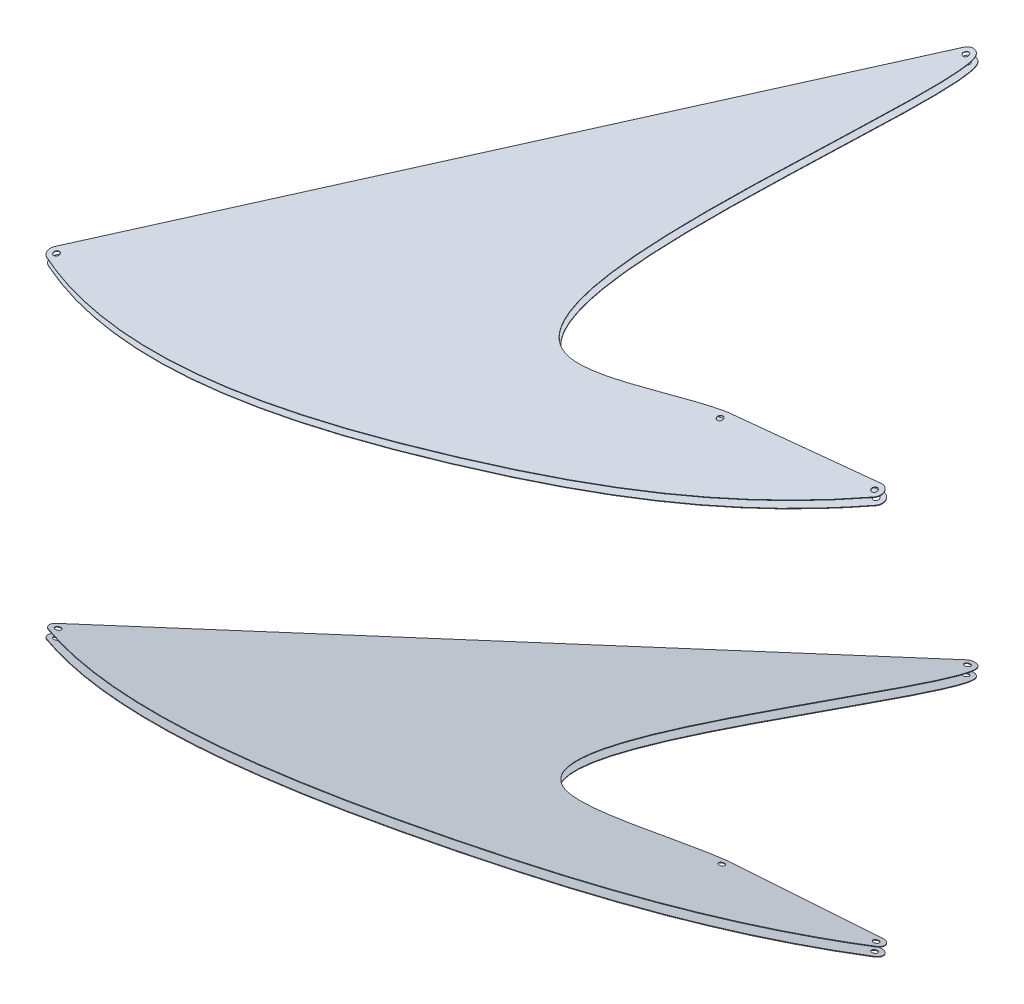
SolidWorks part; units mm, degrees
material "Thornel Mat VMA"
ref_plane "Płaszczyzna XY" through (0, 0, 0) normal (0, 0, 1) x (1, 0, 0)
ref_plane "Płaszczyzna XZ" through (0, 0, 0) normal (0, 1, 0) x (1, 0, 0)
ref_plane "Płaszczyzna YZ" through (0, 0, 0) normal (1, 0, 0) x (0, 0, -1)
sketch "Szkic1" plane through (0, -365.9457, 71.1326) normal (0, -0.9816, 0.1908) x (1, 0, 0)
  line L2 (1483.1737, 808.8534) -> (1634.8716, 794.9597)
  line L3 (939.3713, 984.0725) -> (1348.4905, 414.167)
  line L4 (1483.1737, 808.8534) -> (1634.8716, 794.9597)
  line L5 (939.3713, 984.0725) -> (1348.4905, 414.167)
  circle A0 centre (1354.9893, 418.8323) radius 3 construction
  circle A1 centre (945.8701, 988.7378) radius 3 construction
  circle A2 centre (1634.8716, 802.9597) radius 3 construction
  arc A3 (1634.8716, 794.9597) -> (1640.2813, 808.8534) centre (1634.8716, 802.9597) ccw
  arc A4 (942.8113, 996.1299) -> (939.3713, 984.0725) centre (945.8701, 988.7378) ccw
  arc A5 (1348.4905, 414.167) -> (1362.2836, 415.547) centre (1354.9893, 418.8323) ccw
  arc A6 (1634.8716, 794.9597) -> (1640.2813, 808.8534) centre (1634.8716, 802.9597) ccw
  arc A7 (942.8113, 996.1299) -> (939.3713, 984.0725) centre (945.8701, 988.7378) ccw
  arc A8 (1348.4905, 414.167) -> (1362.2836, 415.547) centre (1354.9893, 418.8323) ccw
  circle A9 centre (1483.9034, 816.82) radius 3 construction
  circle A10 centre (1354.9893, 418.8323) radius 3
  circle A11 centre (945.8701, 988.7378) radius 3
  circle A12 centre (1634.8716, 802.9597) radius 3
  circle A13 centre (1483.9034, 816.82) radius 3
  spline S2 degree 3 poles (1520.5342, -3126.9675) (2189.7267, 400.5932) (1623.1132, 1133.0097) (131.586, 1143.129) (1370.7562, -2890.8231) knots -1.798861 -1.798861 -1.798861 -1.798861 0.451675 2.51583 2.51583 2.51583 2.51583 only from (1640.2813, 808.8534) to (942.8113, 996.1299)
  spline S3 degree 3 poles (-593.8451, 3903.582) (1564.5938, -68.6382) (1362.4748, 333.0797) (1238.3707, 1132.1156) (2251.5927, 131.511) (-793.1853, 4086.8611) knots -1.060105 -1.060105 -1.060105 -1.060105 0.358357 0.741721 1.892324 1.892324 1.892324 1.892324 only from (1362.2836, 415.547) to (1483.1737, 808.8534)
  spline S4 degree 3 poles (1640.2813, 808.8534) (1556.4999, 885.756) (1335.8064, 985.7121) (1065.4306, 1046.8696) (942.8113, 996.1299) knots 0 0 0 0 0.451675 1 1 1 1
  spline S5 degree 3 poles (1362.2836, 415.547) (1370.5074, 433.8062) (1317.9137, 619.9831) (1275.8792, 890.62) (1437.4698, 816.5628) (1483.1737, 808.8534) knots 0 0 0 0 0.358357 0.741721 1 1 1 1
  dimension "D1" = 0
extrude "Dodanie-wyciągnięcie1" add sketch "Szkic1" along normal blind 0.6
sketch "Szkic2" plane through (0, -358.0927, 69.6062) normal (0, 0.9816, -0.1908) x (1, 0, 0)
  line L2 (1634.8716, -794.9597) -> (1483.1737, -808.8534)
  line L3 (1348.4905, -414.167) -> (939.3713, -984.0725)
  line L4 (1634.8716, -794.9597) -> (1483.1737, -808.8534)
  line L5 (1348.4905, -414.167) -> (939.3713, -984.0725)
  circle A0 centre (1354.9893, -418.8323) radius 3 construction
  circle A1 centre (1634.8716, -802.9597) radius 3 construction
  circle A2 centre (1483.9034, -816.82) radius 3 construction
  arc A3 (1362.2836, -415.547) -> (1348.4905, -414.167) centre (1354.9893, -418.8323) ccw
  arc A4 (939.3713, -984.0725) -> (942.8113, -996.1299) centre (945.8701, -988.7378) ccw
  arc A5 (1640.2813, -808.8534) -> (1634.8716, -794.9597) centre (1634.8716, -802.9597) ccw
  arc A6 (1362.2836, -415.547) -> (1348.4905, -414.167) centre (1354.9893, -418.8323) ccw
  arc A7 (939.3713, -984.0725) -> (942.8113, -996.1299) centre (945.8701, -988.7378) ccw
  arc A8 (1640.2813, -808.8534) -> (1634.8716, -794.9597) centre (1634.8716, -802.9597) ccw
  circle A9 centre (945.8701, -988.7378) radius 3 construction
  circle A10 centre (1354.9893, -418.8323) radius 3
  circle A11 centre (1634.8716, -802.9597) radius 3
  circle A12 centre (1483.9034, -816.82) radius 3
  circle A13 centre (945.8701, -988.7378) radius 3
  spline S2 degree 3 poles (-793.3185, -4087.0342) (2251.6149, -131.4891) (1238.37, -1132.1201) (1362.4742, -333.0834) (1564.5907, 68.6321) (-593.7833, -3903.4682) knots -0.89234 -0.89234 -0.89234 -0.89234 0.258279 0.641643 2.060091 2.060091 2.060091 2.060091 only from (1483.1737, -808.8534) to (1362.2836, -415.547)
  spline S3 degree 3 poles (1370.7818, 2890.9066) (131.5761, -1143.1291) (1623.1066, -1133.0121) (2189.723, -400.5978) (1520.5465, 3126.9029) knots -1.515845 -1.515845 -1.515845 -1.515845 0.548325 2.798847 2.798847 2.798847 2.798847 only from (942.8113, -996.1299) to (1640.2813, -808.8534)
  spline S4 degree 3 poles (1483.1737, -808.8534) (1437.4698, -816.5628) (1275.8792, -890.62) (1317.9137, -619.9831) (1370.5074, -433.8062) (1362.2836, -415.547) knots 0 0 0 0 0.258279 0.641643 1 1 1 1
  spline S5 degree 3 poles (942.8113, -996.1299) (1065.4306, -1046.8696) (1335.8064, -985.7121) (1556.4999, -885.756) (1640.2813, -808.8534) knots 0 0 0 0 0.548325 1 1 1 1
  dimension "D1" = 0
extrude "Dodanie-wyciągnięcie2" add sketch "Szkic2" along normal blind 0.6 separate body
mirror "Lustro1" about plane through (0, 0, 0) normal (0, 1, 0) of bodies 102 103
